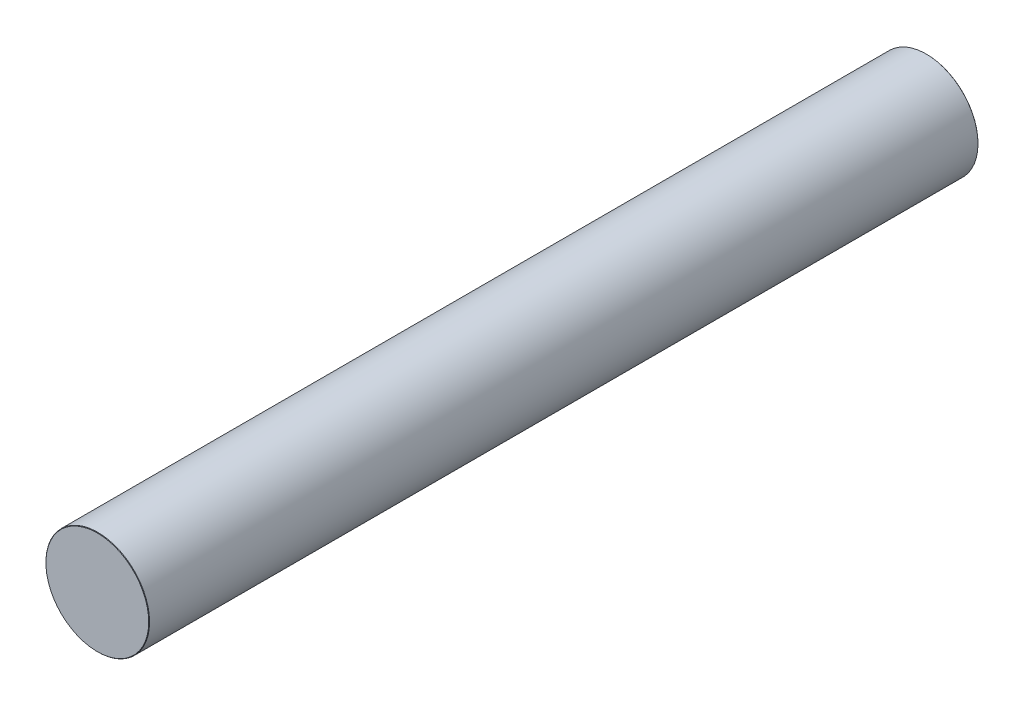
SolidWorks part; units mm, degrees
material "АД 31 ГОСТ 4784-97"
ref_plane "Plane1" through (0, 0, 0) normal (0, 0, 1) x (1, 0, 0)
ref_plane "Plane2" through (0, 0, 0) normal (0, 1, 0) x (1, 0, 0)
ref_plane "Plane3" through (0, 0, 0) normal (1, 0, 0) x (0, 0, -1)
sketch "Эскиз1" plane through (0, 0, 0) normal (0, 0, 1) x (1, 0, 0)
  circle A0 centre (0, 0) radius 12.5
  dimension "D1" = 25
extrude "Бобышка-Вытянуть1" add sketch "Эскиз1" along normal blind 200
chamfer "Фаска1" distance 0.1 angle 45 2 edges at (12.5, 0, 0) (12.5, 0, 200)
